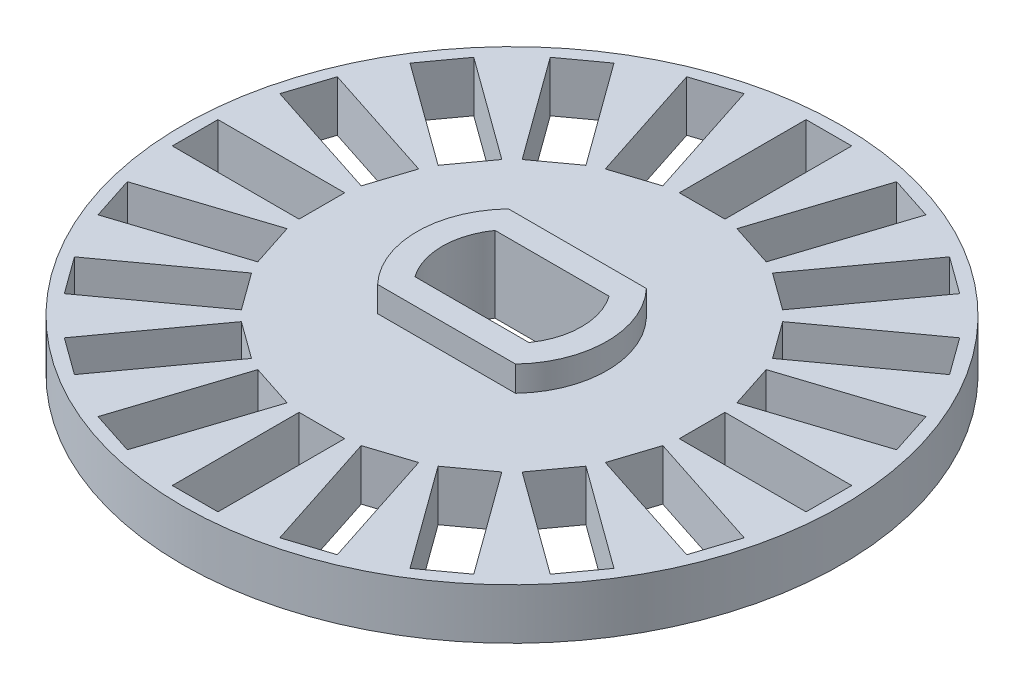
SolidWorks part; units mm, degrees
ref_plane "Front Plane" through (0, 0, 0) normal (0, 0, 1) x (1, 0, 0)
ref_plane "Top Plane" through (0, 0, 0) normal (0, 1, 0) x (1, 0, 0)
ref_plane "Right Plane" through (0, 0, 0) normal (1, 0, 0) x (0, 0, -1)
sketch "Sketch1" plane through (0, 0, 0) normal (0, 1, 0) x (1, 0, 0)
  line L0 (-2.25, 1.5811) -> (2.25, 1.5811)
  line L1 (-2.25, -1.5811) -> (2.25, -1.5811)
  line L2 (1.4617, 7.411) -> (3.0068, 12.1663)
  line L3 (-0.9, 7.5) -> (0.9, 7.5)
  line L4 (-0.9, 7.5) -> (-0.9, 12.5)
  line L5 (-0.9, 12.5) -> (0.9, 12.5)
  line L6 (0.9, 7.5) -> (0.9, 12.5)
  line L7 (-0.9, 7.5) -> (0.9, 12.5) construction
  line L8 (-0.9, 12.5) -> (0.9, 7.5) construction
  line L9 (1.4617, 7.411) -> (3.1736, 6.8548)
  line L10 (3.1736, 6.8548) -> (4.7187, 11.6101)
  line L11 (3.0068, 12.1663) -> (4.7187, 11.6101)
  line L12 (3.6803, 6.5966) -> (6.6192, 10.6417)
  line L13 (3.6803, 6.5966) -> (5.1365, 5.5386)
  line L14 (5.1365, 5.5386) -> (8.0754, 9.5837)
  line L15 (6.6192, 10.6417) -> (8.0754, 9.5837)
  line L16 (5.5386, 5.1365) -> (9.5837, 8.0754)
  line L17 (5.5386, 5.1365) -> (6.5966, 3.6803)
  line L18 (6.5966, 3.6803) -> (10.6417, 6.6192)
  line L19 (9.5837, 8.0754) -> (10.6417, 6.6192)
  line L20 (6.8548, 3.1736) -> (11.6101, 4.7187)
  line L21 (6.8548, 3.1736) -> (7.411, 1.4617)
  line L22 (7.411, 1.4617) -> (12.1663, 3.0068)
  line L23 (11.6101, 4.7187) -> (12.1663, 3.0068)
  line L24 (7.5, 0.9) -> (12.5, 0.9)
  line L25 (7.5, 0.9) -> (7.5, -0.9)
  line L26 (7.5, -0.9) -> (12.5, -0.9)
  line L27 (12.5, 0.9) -> (12.5, -0.9)
  line L28 (7.411, -1.4617) -> (12.1663, -3.0068)
  line L29 (7.411, -1.4617) -> (6.8548, -3.1736)
  line L30 (6.8548, -3.1736) -> (11.6101, -4.7187)
  line L31 (12.1663, -3.0068) -> (11.6101, -4.7187)
  line L32 (6.5966, -3.6803) -> (10.6417, -6.6192)
  line L33 (6.5966, -3.6803) -> (5.5386, -5.1365)
  line L34 (5.5386, -5.1365) -> (9.5837, -8.0754)
  line L35 (10.6417, -6.6192) -> (9.5837, -8.0754)
  line L36 (5.1365, -5.5386) -> (8.0754, -9.5837)
  line L37 (5.1365, -5.5386) -> (3.6803, -6.5966)
  line L38 (3.6803, -6.5966) -> (6.6192, -10.6417)
  line L39 (8.0754, -9.5837) -> (6.6192, -10.6417)
  line L40 (3.1736, -6.8548) -> (4.7187, -11.6101)
  line L41 (3.1736, -6.8548) -> (1.4617, -7.411)
  line L42 (1.4617, -7.411) -> (3.0068, -12.1663)
  line L43 (4.7187, -11.6101) -> (3.0068, -12.1663)
  line L44 (0.9, -7.5) -> (0.9, -12.5)
  line L45 (0.9, -7.5) -> (-0.9, -7.5)
  line L46 (-0.9, -7.5) -> (-0.9, -12.5)
  line L47 (0.9, -12.5) -> (-0.9, -12.5)
  line L48 (-1.4617, -7.411) -> (-3.0068, -12.1663)
  line L49 (-1.4617, -7.411) -> (-3.1736, -6.8548)
  line L50 (-3.1736, -6.8548) -> (-4.7187, -11.6101)
  line L51 (-3.0068, -12.1663) -> (-4.7187, -11.6101)
  line L52 (-3.6803, -6.5966) -> (-6.6192, -10.6417)
  line L53 (-3.6803, -6.5966) -> (-5.1365, -5.5386)
  line L54 (-5.1365, -5.5386) -> (-8.0754, -9.5837)
  line L55 (-6.6192, -10.6417) -> (-8.0754, -9.5837)
  line L56 (-5.5386, -5.1365) -> (-9.5837, -8.0754)
  line L57 (-5.5386, -5.1365) -> (-6.5966, -3.6803)
  line L58 (-6.5966, -3.6803) -> (-10.6417, -6.6192)
  line L59 (-9.5837, -8.0754) -> (-10.6417, -6.6192)
  line L60 (-6.8548, -3.1736) -> (-11.6101, -4.7187)
  line L61 (-6.8548, -3.1736) -> (-7.411, -1.4617)
  line L62 (-7.411, -1.4617) -> (-12.1663, -3.0068)
  line L63 (-11.6101, -4.7187) -> (-12.1663, -3.0068)
  line L64 (-7.5, -0.9) -> (-12.5, -0.9)
  line L65 (-7.5, -0.9) -> (-7.5, 0.9)
  line L66 (-7.5, 0.9) -> (-12.5, 0.9)
  line L67 (-12.5, -0.9) -> (-12.5, 0.9)
  line L68 (-7.411, 1.4617) -> (-12.1663, 3.0068)
  line L69 (-7.411, 1.4617) -> (-6.8548, 3.1736)
  line L70 (-6.8548, 3.1736) -> (-11.6101, 4.7187)
  line L71 (-12.1663, 3.0068) -> (-11.6101, 4.7187)
  line L72 (-6.5966, 3.6803) -> (-10.6417, 6.6192)
  line L73 (-6.5966, 3.6803) -> (-5.5386, 5.1365)
  line L74 (-5.5386, 5.1365) -> (-9.5837, 8.0754)
  line L75 (-10.6417, 6.6192) -> (-9.5837, 8.0754)
  line L76 (-5.1365, 5.5386) -> (-8.0754, 9.5837)
  line L77 (-5.1365, 5.5386) -> (-3.6803, 6.5966)
  line L78 (-3.6803, 6.5966) -> (-6.6192, 10.6417)
  line L79 (-8.0754, 9.5837) -> (-6.6192, 10.6417)
  line L80 (-3.1736, 6.8548) -> (-4.7187, 11.6101)
  line L81 (-3.1736, 6.8548) -> (-1.4617, 7.411)
  line L82 (-1.4617, 7.411) -> (-3.0068, 12.1663)
  line L83 (-4.7187, 11.6101) -> (-3.0068, 12.1663)
  circle A0 centre (0, 0) radius 13
  arc A1 (-2.25, 1.5811) -> (-2.25, -1.5811) centre (0, 0) ccw
  arc A2 (2.25, -1.5811) -> (2.25, 1.5811) centre (0, 0) ccw
  point P3 (0, 10)
  point P90 (0, 0)
  dimension "D1" = 26
  dimension "D2" = 5.5
  dimension "D3" = 4.5
  dimension "D4" = 4.5
  dimension "D5" = 1.8
  dimension "D6" = 0
  dimension "D7" = 5
  dimension "D8" = 7.5
  dimension "D9" = 20
extrude "Boss-Extrude1" add sketch "Sketch1" along normal blind 2 contours A0 A2 L1 A1 L0 L80 L83 L82 L81 L76 L79 L78 L77 L72 L75 L74 L73 L68 L71 L70 L69 L64 L67 L66 L65 L60 L63 L62 L61 L56 L59 L58 L57 L52 L55 L54 L53 L48 L51 L50 L49
sketch "Sketch2" plane through (0, 2, 0) normal (0, 1, 0) x (1, 0, 0)
  line L0 (-2.25, -1.5811) -> (2.25, -1.5811) construction
  line L1 (-2.25, 1.5811) -> (2.25, 1.5811) construction
  line L2 (-2.25, -1.5811) -> (2.25, -1.5811)
  line L3 (-2.25, 1.5811) -> (2.25, 1.5811)
  line L4 (-2.7203, -2.5811) -> (2.7203, -2.5811)
  line L5 (-2.7203, 2.5811) -> (2.7203, 2.5811)
  arc A0 (-2.25, 1.5811) -> (-2.25, -1.5811) centre (0, 0) ccw construction
  arc A1 (2.25, -1.5811) -> (2.25, 1.5811) centre (0, 0) ccw construction
  arc A3 (-2.25, 1.5811) -> (-2.25, -1.5811) centre (0, 0) ccw
  arc A4 (2.25, -1.5811) -> (2.25, 1.5811) centre (0, 0) ccw
  arc A5 (2.7203, -2.5811) -> (2.7203, 2.5811) centre (0, 0) ccw
  arc A6 (-2.7203, 2.5811) -> (-2.7203, -2.5811) centre (0, 0) ccw
  dimension "D1" = 1
extrude "Boss-Extrude2" add sketch "Sketch2" along normal blind 1
